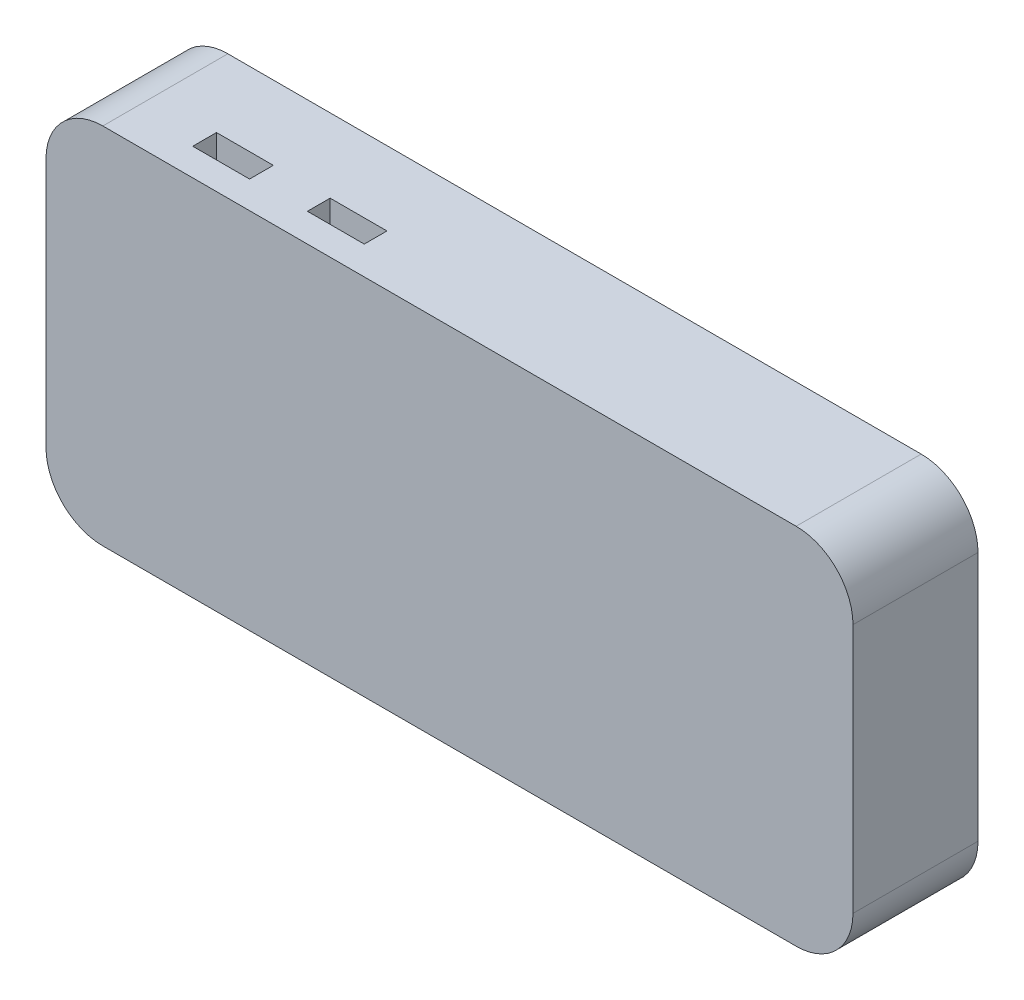
SolidWorks part; units mm, degrees
ref_plane "Front Plane" through (0, 0, 0) normal (0, 0, 1) x (1, 0, 0)
ref_plane "Top Plane" through (0, 0, 0) normal (0, 1, 0) x (1, 0, 0)
ref_plane "Right Plane" through (0, 0, 0) normal (1, 0, 0) x (0, 0, -1)
sketch "Sketch1" plane through (0, 0, 0) normal (0, 0, 1) x (1, 0, 0)
  line L1 (-61, 32) -> (61, 32)
  line L2 (-71, 22) -> (-71, -22)
  line L3 (-61, -32) -> (61, -32)
  line L4 (71, 22) -> (71, -22)
  arc A0 (71, -22) -> (61, -32) centre (61, -22) cw
  arc A1 (71, 22) -> (61, 32) centre (61, 22) ccw
  arc A2 (-61, -32) -> (-71, -22) centre (-61, -22) cw
  arc A3 (-71, 22) -> (-61, 32) centre (-61, 22) cw
  dimension "D5" = 10
  dimension "D1" = 64
  dimension "D2" = 32
  dimension "D3" = 142
  dimension "D4" = 71
extrude "Boss-Extrude1" add sketch "Sketch1" along normal blind 22
sketch "Sketch2" plane through (-71, 0, 0) normal (-1, 0, 0) x (0, 0, 1)
  line L0 (22, 32) -> (0, 32) construction
  line L1 (13, 26) -> (18, 26)
  line L2 (13, 26) -> (13, 13)
  line L3 (13, 13) -> (18, 13)
  line L4 (18, 26) -> (18, 13)
  line L5 (4, 26) -> (9, 26)
  line L6 (4, 26) -> (4, 13)
  line L7 (4, 13) -> (9, 13)
  line L8 (9, 26) -> (9, 13)
  line L9 (22, 22) -> (22, 32) construction
  line L10 (0, 22) -> (0, -22) construction
  dimension "D1" = 6
  dimension "D2" = 4
  dimension "D3" = 5
  dimension "D4" = 13
  dimension "D5" = 13
  dimension "D6" = 4
  dimension "D7" = 5
extrude "Cut-Extrude1" cut sketch "Sketch2" against normal blind 10
sketch "Sketch3" plane through (0, 32, 0) normal (0, 1, 0) x (1, 0, 0)
  line L0 (-71, -11) -> (71, -11) construction
  line L1 (-71, -13) -> (-71, -9) construction
  line L2 (71, -22) -> (71, 0) construction
  line L4 (-30, -13) -> (-20, -13)
  line L5 (-30, -13) -> (-30, -17)
  line L6 (-30, -17) -> (-20, -17)
  line L7 (-20, -13) -> (-20, -17)
  line L8 (-40, -13) -> (-50, -13)
  line L9 (-40, -13) -> (-40, -17.1784)
  line L10 (-40, -17.1784) -> (-50, -17.1784)
  line L11 (-50, -13) -> (-50, -17.1784)
  point P14 (-25, -13)
  point P15 (-30, -15)
  dimension "D1" = 21
  dimension "D2" = 4
  dimension "D3" = 10
  dimension "D4" = 2
  dimension "D5" = 10
  dimension "D6" = 10
extrude "Cut-Extrude2" cut sketch "Sketch3" against normal blind 5
